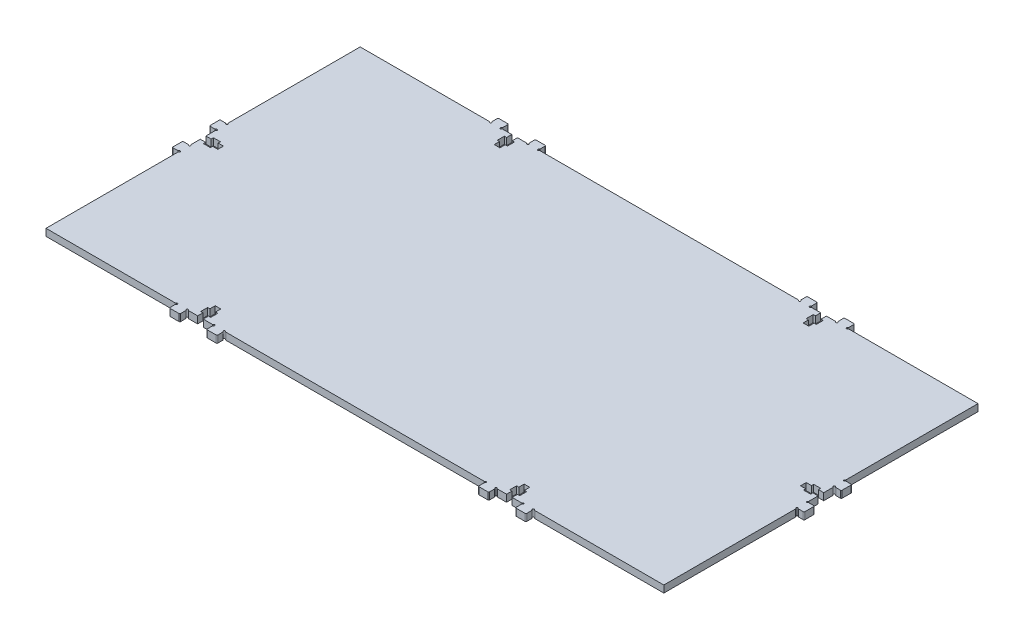
SolidWorks part; units mm, degrees
ref_plane "Alzado" through (0, 0, 0) normal (0, 0, 1) x (1, 0, 0)
ref_plane "Planta" through (0, 0, 0) normal (0, 1, 0) x (1, 0, 0)
ref_plane "Vista lateral" through (0, 0, 0) normal (1, 0, 0) x (0, 0, -1)
sketch "Croquis1" plane through (0, 0, 0) normal (0, 1, 0) x (1, 0, 0)
  line L5 (-176, 89.5) -> (176, -89.5) construction
  line L6 (-176, -89.5) -> (176, 89.5) construction
  line L8 (-176, 44.75) -> (176, 44.75) construction
  line L10 (-176, -44.75) -> (176, -44.75) construction
  line L27 (-176.866, -13.6) -> (-179.5001, -13.6)
  line L50 (-176, -14.4661) -> (-176, -89.5)
  line L53 (0, 89.5) -> (0, 99.5) construction
  line L73 (176, 1.6) -> (176, -1.6) construction
  line L94 (74.4, 90.366) -> (74.4, 93.1701)
  line L95 (74.9, 93.6701) -> (79.9, 93.6701)
  line L96 (88, 89.5) -> (88, -89.5) construction
  line L97 (80.4, 93.1701) -> (80.4, 90.366)
  line L98 (-88, 89.5) -> (-88, -89.5) construction
  line L99 (86.4, 89.5) -> (86.4, 86.5)
  line L100 (86.4, 86.5) -> (85.125, 86.5)
  line L101 (85.125, 86.5) -> (85.125, 82.5)
  line L102 (85.125, 82.5) -> (86.4, 82.5)
  line L103 (86.4, 82.5) -> (86.4, 79.5)
  line L104 (86.4, 79.5) -> (89.6, 79.5)
  line L105 (89.6, 79.5) -> (89.6, 82.5)
  line L106 (89.6, 82.5) -> (90.875, 82.5)
  line L107 (90.875, 82.5) -> (90.875, 86.5)
  line L108 (90.875, 86.5) -> (89.6, 86.5)
  line L109 (89.6, 86.5) -> (89.6, 89.5)
  line L111 (95.6, 90.366) -> (95.6, 93.1701)
  line L112 (96.1, 93.6701) -> (101.1, 93.6701)
  line L113 (101.6, 93.1701) -> (101.6, 90.366)
  line L114 (88, 79.5) -> (88, 89.5) construction
  line L116 (-89.6, 86.5) -> (-90.875, 86.5)
  line L117 (-74.4, 93.1701) -> (-74.4, 90.366)
  line L118 (-90.875, 86.5) -> (-90.875, 82.5)
  line L119 (-101.1, 93.6701) -> (-96.1, 93.6701)
  line L120 (-89.6, 82.5) -> (-89.6, 79.5)
  line L121 (-89.6, 79.5) -> (-86.4, 79.5)
  line L122 (-90.875, 82.5) -> (-89.6, 82.5)
  line L123 (-86.4, 86.5) -> (-86.4, 89.5)
  line L124 (-88, 79.5) -> (-88, 89.5) construction
  line L125 (-89.6, 89.5) -> (-89.6, 86.5)
  line L126 (-85.125, 82.5) -> (-85.125, 86.5)
  line L127 (-101.6, 90.366) -> (-101.6, 93.1701)
  line L128 (-86.4, 82.5) -> (-85.125, 82.5)
  line L129 (-85.125, 86.5) -> (-86.4, 86.5)
  line L130 (-80.4, 90.366) -> (-80.4, 93.1701)
  line L132 (-79.9, 93.6701) -> (-74.9, 93.6701)
  line L133 (-95.6, 93.1701) -> (-95.6, 90.366)
  line L135 (-86.4, 79.5) -> (-86.4, 82.5)
  line L140 (-176, 0) -> (176, 0) construction
  line L141 (-180.0001, -13.1) -> (-180.0001, -8.1)
  line L142 (-179.5001, -7.6) -> (-176.866, -7.6)
  line L143 (-176, -1.6) -> (-173, -1.6)
  line L144 (-173, -1.6) -> (-173, -2.875)
  line L145 (-173, -2.875) -> (-169, -2.875)
  line L146 (-169, -2.875) -> (-169, -1.6)
  line L147 (-169, -1.6) -> (-166, -1.6)
  line L148 (-166, -1.6) -> (-166, 1.6)
  line L149 (-166, 1.6) -> (-169, 1.6)
  line L150 (-169, 1.6) -> (-169, 2.875)
  line L151 (-169, 2.875) -> (-173, 2.875)
  line L152 (-173, 2.875) -> (-173, 1.6)
  line L153 (-173, 1.6) -> (-176, 1.6)
  line L154 (-176, 1.6) -> (-176, 6.734)
  line L155 (-176.866, 7.6) -> (-179.5001, 7.6)
  line L156 (-180.0001, 8.1) -> (-180.0001, 13.1)
  line L157 (-179.5001, 13.6) -> (-176.866, 13.6)
  line L158 (-176, -1.6) -> (-176, -6.734)
  line L161 (176, -14.4661) -> (176, -89.5)
  line L162 (176, -1.6) -> (176, -6.734)
  line L163 (179.5001, 13.6) -> (176.866, 13.6)
  line L164 (180.0001, 8.1) -> (180.0001, 13.1)
  line L165 (176.866, 7.6) -> (179.5001, 7.6)
  line L166 (176, 1.6) -> (176, 6.734)
  line L167 (173, 1.6) -> (176, 1.6)
  line L168 (173, 2.875) -> (173, 1.6)
  line L169 (169, 2.875) -> (173, 2.875)
  line L170 (169, 1.6) -> (169, 2.875)
  line L171 (166, 1.6) -> (169, 1.6)
  line L172 (166, -1.6) -> (166, 1.6)
  line L173 (169, -1.6) -> (166, -1.6)
  line L174 (169, -2.875) -> (169, -1.6)
  line L175 (173, -2.875) -> (169, -2.875)
  line L176 (173, -1.6) -> (173, -2.875)
  line L177 (176, -1.6) -> (173, -1.6)
  line L178 (179.5001, -7.6) -> (176.866, -7.6)
  line L179 (180.0001, -13.1) -> (180.0001, -8.1)
  line L181 (176.866, -13.6) -> (179.5001, -13.6)
  line L182 (-88, -79.5) -> (-88, -89.5) construction
  line L183 (88, -79.5) -> (88, -89.5) construction
  line L184 (-73.534, -89.5) -> (73.534, -89.5)
  line L185 (102.466, -89.5) -> (176, -89.5)
  line L186 (89.6, -89.5) -> (94.734, -89.5)
  line L187 (-94.734, -89.5) -> (-89.6, -89.5)
  line L188 (-86.4, -79.5) -> (-86.4, -82.5)
  line L189 (-86.4, -89.5) -> (-81.266, -89.5)
  line L190 (-95.6, -93.1701) -> (-95.6, -90.366)
  line L191 (-79.9, -93.6701) -> (-74.9, -93.6701)
  line L192 (81.266, -89.5) -> (86.4, -89.5)
  line L193 (-80.4, -90.366) -> (-80.4, -93.1701)
  line L194 (-85.125, -86.5) -> (-86.4, -86.5)
  line L195 (-86.4, -82.5) -> (-85.125, -82.5)
  line L196 (-101.6, -90.366) -> (-101.6, -93.1701)
  line L197 (-85.125, -82.5) -> (-85.125, -86.5)
  line L198 (-89.6, -89.5) -> (-89.6, -86.5)
  line L199 (-86.4, -86.5) -> (-86.4, -89.5)
  line L200 (-90.875, -82.5) -> (-89.6, -82.5)
  line L201 (-89.6, -79.5) -> (-86.4, -79.5)
  line L202 (-89.6, -82.5) -> (-89.6, -79.5)
  line L203 (-101.1, -93.6701) -> (-96.1, -93.6701)
  line L204 (-90.875, -86.5) -> (-90.875, -82.5)
  line L205 (-74.4, -93.1701) -> (-74.4, -90.366)
  line L206 (-89.6, -86.5) -> (-90.875, -86.5)
  line L207 (101.6, -93.1701) -> (101.6, -90.366)
  line L208 (96.1, -93.6701) -> (101.1, -93.6701)
  line L209 (95.6, -90.366) -> (95.6, -93.1701)
  line L210 (89.6, -86.5) -> (89.6, -89.5)
  line L211 (90.875, -86.5) -> (89.6, -86.5)
  line L212 (90.875, -82.5) -> (90.875, -86.5)
  line L213 (89.6, -82.5) -> (90.875, -82.5)
  line L214 (89.6, -79.5) -> (89.6, -82.5)
  line L215 (86.4, -79.5) -> (89.6, -79.5)
  line L216 (86.4, -82.5) -> (86.4, -79.5)
  line L217 (85.125, -82.5) -> (86.4, -82.5)
  line L218 (85.125, -86.5) -> (85.125, -82.5)
  line L219 (86.4, -86.5) -> (85.125, -86.5)
  line L220 (86.4, -89.5) -> (86.4, -86.5)
  line L221 (80.4, -93.1701) -> (80.4, -90.366)
  line L222 (74.9, -93.6701) -> (79.9, -93.6701)
  line L223 (74.4, -90.366) -> (74.4, -93.1701)
  line L225 (-94.734, 89.5) -> (-89.6, 89.5)
  line L226 (-176, 89.5) -> (-102.466, 89.5)
  line L227 (-176, 89.5) -> (-176, 14.466)
  line L228 (-176, -89.5) -> (-102.466, -89.5)
  line L229 (176, 89.5) -> (176, 14.466)
  line L230 (-86.4, 89.5) -> (-81.266, 89.5)
  line L231 (-73.534, 89.5) -> (73.534, 89.5)
  line L232 (81.266, 89.5) -> (86.4, 89.5)
  line L233 (89.6, 89.5) -> (94.734, 89.5)
  line L234 (0, -89.5) -> (0, -99.5) construction
  line L235 (102.466, 89.5) -> (176, 89.5)
  arc A64 (73.967, 89.25) -> (73.534, 89.5) centre (73.534, 89) ccw
  arc A65 (73.967, 89.25) -> (74.65, 89.933) centre (74.4, 89.5) ccw
  arc A66 (74.4, 90.366) -> (74.65, 89.933) centre (74.9, 90.366) ccw
  arc A67 (74.9, 93.6701) -> (74.4, 93.1701) centre (74.9, 93.1701) ccw
  arc A68 (80.4, 93.1701) -> (79.9, 93.6701) centre (79.9, 93.1701) ccw
  arc A69 (80.15, 89.933) -> (80.4, 90.366) centre (79.9, 90.366) ccw
  arc A70 (80.15, 89.933) -> (80.833, 89.25) centre (80.4, 89.5) ccw
  arc A71 (81.266, 89.5) -> (80.833, 89.25) centre (81.266, 89) ccw
  arc A72 (95.167, 89.25) -> (94.734, 89.5) centre (94.734, 89) ccw
  arc A73 (95.167, 89.25) -> (95.85, 89.933) centre (95.6, 89.5) ccw
  arc A74 (95.6, 90.366) -> (95.85, 89.933) centre (96.1, 90.366) ccw
  arc A75 (96.1, 93.6701) -> (95.6, 93.1701) centre (96.1, 93.1701) ccw
  arc A76 (101.6, 93.1701) -> (101.1, 93.6701) centre (101.1, 93.1701) ccw
  arc A77 (101.35, 89.933) -> (101.6, 90.366) centre (101.1, 90.366) ccw
  arc A78 (101.35, 89.933) -> (102.033, 89.25) centre (101.6, 89.5) ccw
  arc A79 (102.466, 89.5) -> (102.033, 89.25) centre (102.466, 89) ccw
  arc A80 (-74.65, 89.933) -> (-74.4, 90.366) centre (-74.9, 90.366) ccw
  arc A81 (-95.85, 89.933) -> (-95.6, 90.366) centre (-96.1, 90.366) ccw
  arc A82 (-102.033, 89.25) -> (-101.35, 89.933) centre (-101.6, 89.5) ccw
  arc A83 (-95.85, 89.933) -> (-95.167, 89.25) centre (-95.6, 89.5) ccw
  arc A84 (-73.534, 89.5) -> (-73.967, 89.25) centre (-73.534, 89) ccw
  arc A85 (-94.734, 89.5) -> (-95.167, 89.25) centre (-94.734, 89) ccw
  arc A86 (-80.4, 90.366) -> (-80.15, 89.933) centre (-79.9, 90.366) ccw
  arc A87 (-101.6, 90.366) -> (-101.35, 89.933) centre (-101.1, 90.366) ccw
  arc A88 (-95.6, 93.1701) -> (-96.1, 93.6701) centre (-96.1, 93.1701) ccw
  arc A89 (-102.033, 89.25) -> (-102.466, 89.5) centre (-102.466, 89) ccw
  arc A90 (-74.65, 89.933) -> (-73.967, 89.25) centre (-74.4, 89.5) ccw
  arc A91 (-80.833, 89.25) -> (-81.266, 89.5) centre (-81.266, 89) ccw
  arc A92 (-79.9, 93.6701) -> (-80.4, 93.1701) centre (-79.9, 93.1701) ccw
  arc A93 (-74.4, 93.1701) -> (-74.9, 93.6701) centre (-74.9, 93.1701) ccw
  arc A94 (-101.1, 93.6701) -> (-101.6, 93.1701) centre (-101.1, 93.1701) ccw
  arc A95 (-80.833, 89.25) -> (-80.15, 89.933) centre (-80.4, 89.5) ccw
  arc A96 (-175.75, -14.033) -> (-176, -14.4661) centre (-175.5, -14.4661) ccw
  arc A97 (-175.75, -14.033) -> (-176.433, -13.35) centre (-176, -13.6) ccw
  arc A98 (-176.866, -13.6) -> (-176.433, -13.35) centre (-176.866, -13.1) ccw
  arc A99 (-180.0001, -13.1) -> (-179.5001, -13.6) centre (-179.5001, -13.1) ccw
  arc A100 (-179.5001, -7.6) -> (-180.0001, -8.1) centre (-179.5001, -8.1) ccw
  arc A101 (-176.433, -7.85) -> (-176.866, -7.6) centre (-176.866, -8.1) ccw
  arc A102 (-176.433, -7.85) -> (-175.75, -7.167) centre (-176, -7.6) ccw
  arc A103 (-176, -6.734) -> (-175.75, -7.167) centre (-175.5, -6.734) ccw
  arc A104 (-175.75, 7.167) -> (-176, 6.734) centre (-175.5, 6.734) ccw
  arc A105 (-175.75, 7.167) -> (-176.433, 7.85) centre (-176, 7.6) ccw
  arc A106 (-176.866, 7.6) -> (-176.433, 7.85) centre (-176.866, 8.1) ccw
  arc A107 (-180.0001, 8.1) -> (-179.5001, 7.6) centre (-179.5001, 8.1) ccw
  arc A108 (-179.5001, 13.6) -> (-180.0001, 13.1) centre (-179.5001, 13.1) ccw
  arc A109 (-176.433, 13.35) -> (-176.866, 13.6) centre (-176.866, 13.1) ccw
  arc A110 (-176.433, 13.35) -> (-175.75, 14.033) centre (-176, 13.6) ccw
  arc A111 (-176, 14.466) -> (-175.75, 14.033) centre (-175.5, 14.466) ccw
  arc A112 (176, 14.466) -> (175.75, 14.033) centre (175.5, 14.466) cw
  arc A113 (176.433, 13.35) -> (175.75, 14.033) centre (176, 13.6) cw
  arc A114 (176.433, 13.35) -> (176.866, 13.6) centre (176.866, 13.1) cw
  arc A115 (179.5001, 13.6) -> (180.0001, 13.1) centre (179.5001, 13.1) cw
  arc A116 (180.0001, 8.1) -> (179.5001, 7.6) centre (179.5001, 8.1) cw
  arc A117 (176.866, 7.6) -> (176.433, 7.85) centre (176.866, 8.1) cw
  arc A118 (175.75, 7.167) -> (176.433, 7.85) centre (176, 7.6) cw
  arc A119 (175.75, 7.167) -> (176, 6.734) centre (175.5, 6.734) cw
  arc A120 (176, -6.734) -> (175.75, -7.167) centre (175.5, -6.734) cw
  arc A121 (176.433, -7.85) -> (175.75, -7.167) centre (176, -7.6) cw
  arc A122 (176.433, -7.85) -> (176.866, -7.6) centre (176.866, -8.1) cw
  arc A123 (179.5001, -7.6) -> (180.0001, -8.1) centre (179.5001, -8.1) cw
  arc A124 (180.0001, -13.1) -> (179.5001, -13.6) centre (179.5001, -13.1) cw
  arc A125 (176.866, -13.6) -> (176.433, -13.35) centre (176.866, -13.1) cw
  arc A126 (175.75, -14.033) -> (176.433, -13.35) centre (176, -13.6) cw
  arc A127 (175.75, -14.033) -> (176, -14.4661) centre (175.5, -14.4661) cw
  arc A128 (-80.833, -89.25) -> (-80.15, -89.933) centre (-80.4, -89.5) cw
  arc A129 (-101.1, -93.6701) -> (-101.6, -93.1701) centre (-101.1, -93.1701) cw
  arc A130 (-74.4, -93.1701) -> (-74.9, -93.6701) centre (-74.9, -93.1701) cw
  arc A131 (-79.9, -93.6701) -> (-80.4, -93.1701) centre (-79.9, -93.1701) cw
  arc A132 (-80.833, -89.25) -> (-81.266, -89.5) centre (-81.266, -89) cw
  arc A133 (-74.65, -89.933) -> (-73.967, -89.25) centre (-74.4, -89.5) cw
  arc A134 (-102.033, -89.25) -> (-102.466, -89.5) centre (-102.466, -89) cw
  arc A135 (-95.6, -93.1701) -> (-96.1, -93.6701) centre (-96.1, -93.1701) cw
  arc A136 (-101.6, -90.366) -> (-101.35, -89.933) centre (-101.1, -90.366) cw
  arc A137 (-80.4, -90.366) -> (-80.15, -89.933) centre (-79.9, -90.366) cw
  arc A138 (-94.734, -89.5) -> (-95.167, -89.25) centre (-94.734, -89) cw
  arc A139 (-73.534, -89.5) -> (-73.967, -89.25) centre (-73.534, -89) cw
  arc A140 (-95.85, -89.933) -> (-95.167, -89.25) centre (-95.6, -89.5) cw
  arc A141 (-102.033, -89.25) -> (-101.35, -89.933) centre (-101.6, -89.5) cw
  arc A142 (-95.85, -89.933) -> (-95.6, -90.366) centre (-96.1, -90.366) cw
  arc A143 (-74.65, -89.933) -> (-74.4, -90.366) centre (-74.9, -90.366) cw
  arc A144 (102.466, -89.5) -> (102.033, -89.25) centre (102.466, -89) cw
  arc A145 (101.35, -89.933) -> (102.033, -89.25) centre (101.6, -89.5) cw
  arc A146 (101.35, -89.933) -> (101.6, -90.366) centre (101.1, -90.366) cw
  arc A147 (101.6, -93.1701) -> (101.1, -93.6701) centre (101.1, -93.1701) cw
  arc A148 (96.1, -93.6701) -> (95.6, -93.1701) centre (96.1, -93.1701) cw
  arc A149 (95.6, -90.366) -> (95.85, -89.933) centre (96.1, -90.366) cw
  arc A150 (95.167, -89.25) -> (95.85, -89.933) centre (95.6, -89.5) cw
  arc A151 (95.167, -89.25) -> (94.734, -89.5) centre (94.734, -89) cw
  arc A152 (81.266, -89.5) -> (80.833, -89.25) centre (81.266, -89) cw
  arc A153 (80.15, -89.933) -> (80.833, -89.25) centre (80.4, -89.5) cw
  arc A154 (80.15, -89.933) -> (80.4, -90.366) centre (79.9, -90.366) cw
  arc A155 (80.4, -93.1701) -> (79.9, -93.6701) centre (79.9, -93.1701) cw
  arc A156 (74.9, -93.6701) -> (74.4, -93.1701) centre (74.9, -93.1701) cw
  arc A157 (74.4, -90.366) -> (74.65, -89.933) centre (74.9, -90.366) cw
  arc A158 (73.967, -89.25) -> (74.65, -89.933) centre (74.4, -89.5) cw
  arc A159 (73.967, -89.25) -> (73.534, -89.5) centre (73.534, -89) cw
  point P0 (0, 0)
  dimension "D1" = 352
  dimension "D2" = 360.0001
extrude "Saliente-Extruir1" add sketch "Croquis1" along normal blind 4
